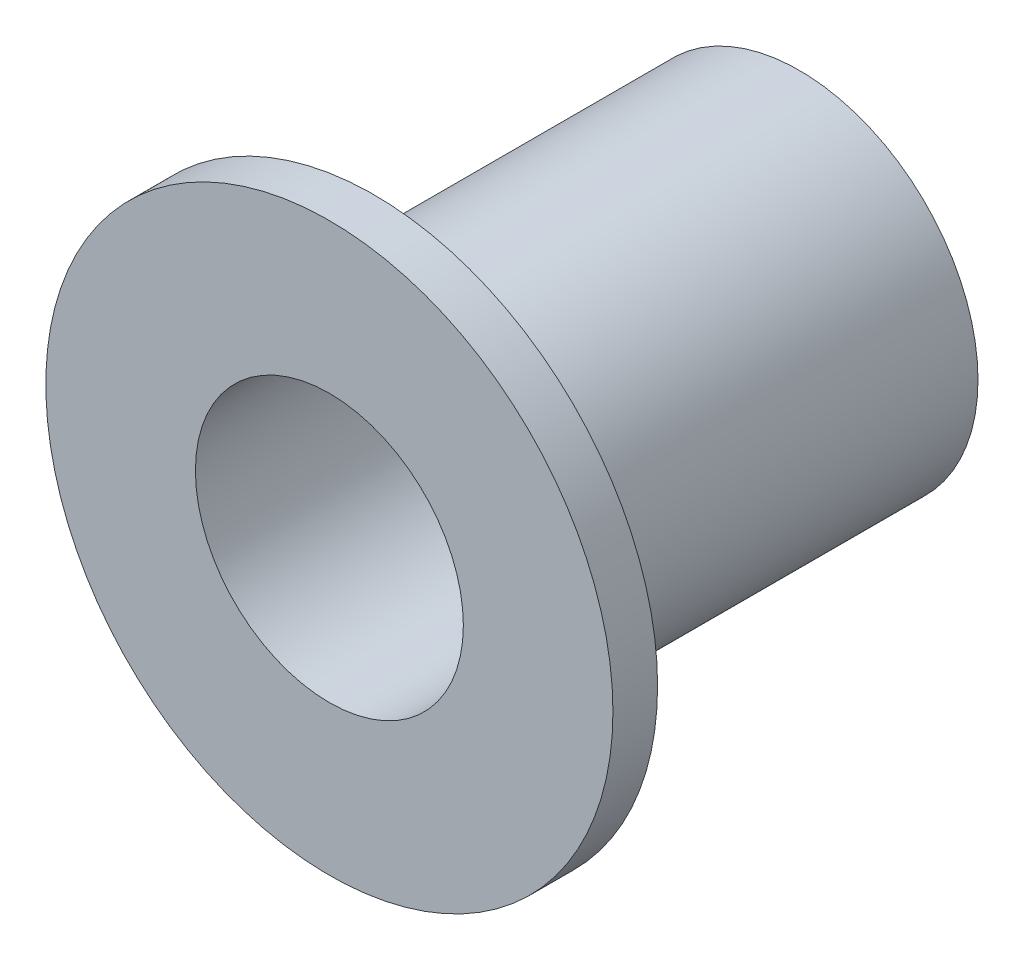
SolidWorks part; units mm, degrees
material "ABS"
ref_plane "Front Plane" through (0, 0, 0) normal (0, 0, 1) x (1, 0, 0)
ref_plane "Top Plane" through (0, 0, 0) normal (0, 1, 0) x (1, 0, 0)
ref_plane "Right Plane" through (0, 0, 0) normal (1, 0, 0) x (0, 0, -1)
sketch "Sketch1" plane through (0, 0, 0) normal (0, 0, 1) x (1, 0, 0)
  circle A0 centre (0, 0) radius 3
  circle A1 centre (0, 0) radius 6.35
  dimension "D1" = 6
  dimension "D2" = 12.7
extrude "Boss-Extrude1" add sketch "Sketch1" along normal blind 1
sketch "Sketch2" plane through (0, 0, 0) normal (0, 0, -1) x (-1, 0, 0)
  circle A0 centre (0, 0) radius 3 construction
  circle A1 centre (0, 0) radius 3
  circle A2 centre (0, 0) radius 4
  dimension "D1" = 8
extrude "Boss-Extrude2" add sketch "Sketch2" along normal blind 9.525
